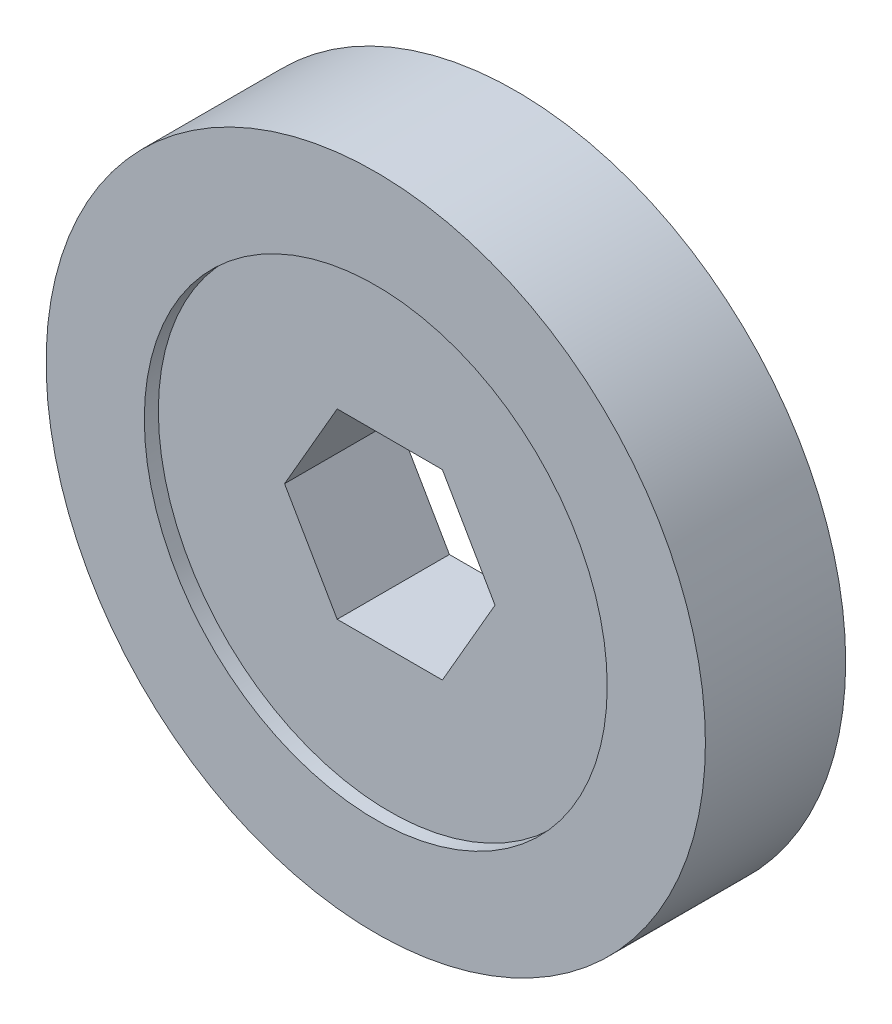
SolidWorks part; units mm, degrees
ref_plane "Plan de face" through (0, 0, 0) normal (0, 0, 1) x (1, 0, 0)
ref_plane "Plan de dessus" through (0, 0, 0) normal (0, 1, 0) x (1, 0, 0)
ref_plane "Plan de droite" through (0, 0, 0) normal (1, 0, 0) x (0, 0, -1)
sketch "Esquisse1" plane through (0, 0, 0) normal (0, 0, 1) x (1, 0, 0)
  circle A1 centre (0, 0) radius 23.5
  dimension "D1" = 47
extrude "Boss.-Extru.1" add sketch "Esquisse1" along normal blind 10
sketch "Esquisse3" plane through (0, 0, 10) normal (0, 0, 1) x (1, 0, 0)
  line L0 (-9.6301, 16.6798) -> (0, 0) construction
  line L1 (0, 0) -> (7.3866, 12.794) construction
  line L2 (-7.5013, 0) -> (-3.7497, 6.4947)
  line L3 (-33.661, 0) -> (16.1541, 0) construction
  line L4 (-3.7497, 6.4947) -> (3.75, 6.4952)
  line L5 (3.75, 6.4952) -> (7.5, 0)
  line L6 (7.5, 0) -> (-7.5013, 0)
  circle A0 centre (0, 0) radius 7.5 construction
  dimension "D1" = 15
  dimension "D2" = 60
  dimension "D3" = 60
extrude "Enlèv. mat.-Extru.1" cut sketch "Esquisse3" against normal blind 10
mirror "Symétrie1" about plane through (0, 0, 0) normal (0, 1, 0) of "Enlèv. mat.-Extru.1"
sketch "Esquisse4" plane through (0, 0, 10) normal (0, 0, 1) x (1, 0, 0)
  circle A0 centre (0, 0) radius 16.5
  dimension "D1" = 33
extrude "Enlèv. mat.-Extru.2" cut sketch "Esquisse4" against normal blind 1
pattern_linear "Répétition linéaire1" count 2 spacing 9 along (0, 0, -1) of "Enlèv. mat.-Extru.2"
